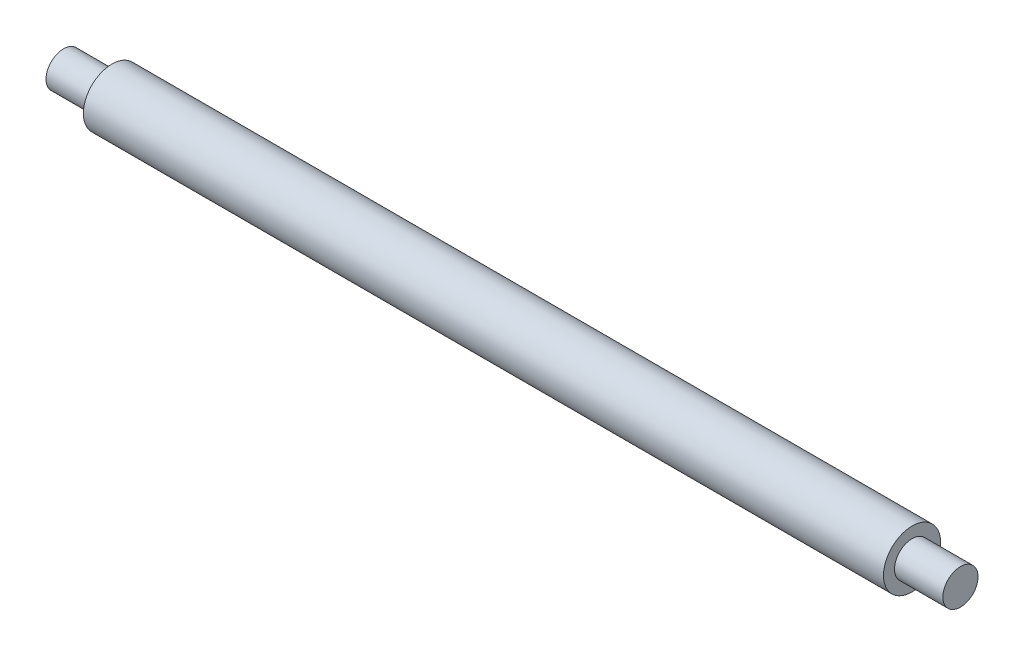
SolidWorks part; units mm, degrees
ref_plane "Front Plane" through (0, 0, 0) normal (0, 0, 1) x (1, 0, 0)
ref_plane "Top Plane" through (0, 0, 0) normal (0, 1, 0) x (1, 0, 0)
ref_plane "Right Plane" through (0, 0, 0) normal (1, 0, 0) x (0, 0, -1)
sketch "Sketch1" plane through (0, 0, 0) normal (0, 0, 1) x (1, 0, 0)
  line L0 (-165.1291, 0) -> (59.4098, 0) construction
  line L1 (-148.2623, 0) -> (-148.2623, 4)
  line L2 (-148.2623, 4) -> (-137.2623, 4)
  line L3 (-137.2623, 4) -> (-137.2623, 6.5)
  line L4 (-137.2623, 6.5) -> (44.7377, 6.5)
  line L5 (44.7377, 6.5) -> (44.7377, 4)
  line L6 (44.7377, 4) -> (55.7377, 4)
  line L7 (55.7377, 4) -> (55.7377, 0)
  line L8 (-148.2623, 0) -> (55.7377, 0)
  dimension "D1" = 4
  dimension "D2" = 6.5
  dimension "D3" = 4
  dimension "D4" = 11
  dimension "D5" = 11
  dimension "D6" = 182
  dimension "D7" = 44.7377
revolve "Revolve1" add sketch "Sketch1" angle 360 about L0
